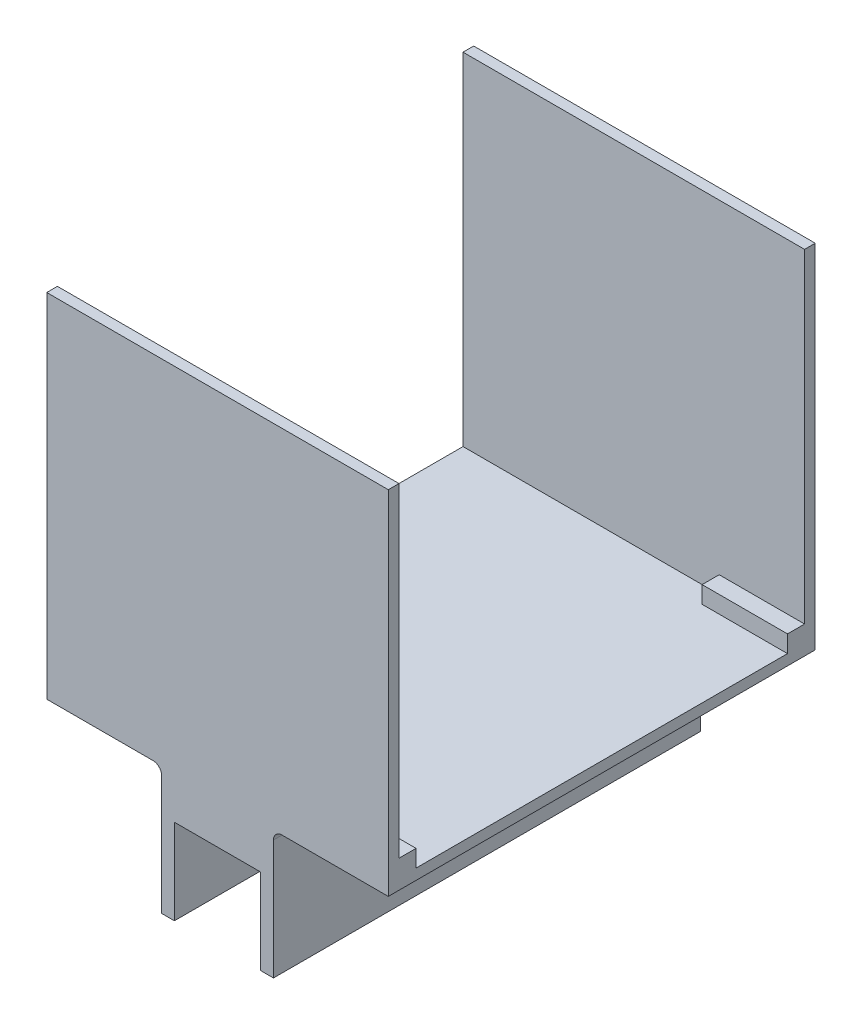
SolidWorks part; units mm, degrees
ref_plane "Front Plane" through (0, 0, 0) normal (0, 0, 1) x (1, 0, 0)
ref_plane "Top Plane" through (0, 0, 0) normal (0, 1, 0) x (1, 0, 0)
ref_plane "Right Plane" through (0, 0, 0) normal (1, 0, 0) x (0, 0, -1)
sketch "Sketch2" plane through (0, 0, 0) normal (0, 0, 1) x (1, 0, 0)
  line L0 (-12.827, -12.7) -> (-16.637, -12.7)
  line L1 (-12.827, -12.7) -> (12.827, -12.7) construction
  line L2 (-12.827, -12.7) -> (-12.827, 12.7)
  line L3 (-12.827, 12.7) -> (12.827, 12.7)
  line L4 (12.827, -12.7) -> (12.827, 12.7)
  line L5 (-12.827, -12.7) -> (12.827, 12.7) construction
  line L6 (-12.827, 12.7) -> (12.827, -12.7) construction
  line L7 (-16.637, -12.7) -> (-16.637, 25.4)
  line L8 (12.827, -12.7) -> (16.637, -12.7)
  line L9 (-16.637, 25.4) -> (16.637, 25.4)
  line L10 (16.637, 25.4) -> (16.637, -12.7)
  point P0 (0, 0)
  dimension "D1" = 25.654
  dimension "D2" = 25.4
  dimension "D3" = 3.81
  dimension "D4" = 38.1
  dimension "D5" = 3.81
extrude "Boss-Extrude1" add sketch "Sketch2" along normal blind 127
sketch "Sketch5" plane through (0, 25.4, 0) normal (0, 1, 0) x (1, 0, 0)
  line L0 (0, 0) -> (0, -127) construction
  line L1 (16.637, -127) -> (-16.637, -127) construction
  line L3 (-50.8, -127) -> (50.8, -127)
  line L4 (-50.8, -127) -> (-50.8, 0)
  line L5 (-50.8, 0) -> (50.8, 0)
  line L6 (50.8, -127) -> (50.8, 0)
  line L7 (-50.8, -127) -> (50.8, 0) construction
  line L8 (-50.8, 0) -> (50.8, -127) construction
  point P5 (0, -63.5)
  dimension "D1" = 101.6
  dimension "D2" = 127
extrude "Boss-Extrude3" add sketch "Sketch5" along normal blind 3.175
fillet "Fillet1" radius 2.54 2 edges at (16.637, 25.4, 63.5) (-16.637, 25.4, 63.5)
sketch "Sketch6" plane through (0, 28.575, 0) normal (0, 1, 0) x (1, 0, 0)
  line L0 (50.8, -127) -> (50.8, 0) construction
  line L1 (-50.8, -127) -> (50.8, -127)
  line L2 (-50.8, -127) -> (-50.8, -123.825)
  line L3 (-50.8, -123.825) -> (50.8, -123.825)
  line L4 (50.8, -127) -> (50.8, -123.825)
  line L6 (-50.8, 0) -> (50.8, 0)
  line L7 (-50.8, 0) -> (-50.8, -3.175)
  line L8 (-50.8, -3.175) -> (50.8, -3.175)
  line L9 (50.8, 0) -> (50.8, -3.175)
  dimension "D1" = 3.175
  dimension "D2" = 3.175
extrude "Boss-Extrude4" add sketch "Sketch6" along normal blind 101.6
sketch "Sketch9" plane through (50.8, 0, 0) normal (1, 0, 0) x (0, 0, -1)
  line L0 (-123.825, 130.175) -> (-123.825, 28.575) construction
  line L1 (-123.825, 28.575) -> (-3.175, 28.575) construction
  line L6 (-3.175, 130.175) -> (-3.175, 28.575) construction
  line L7 (-123.825, 29.9085) -> (-123.825, 28.575)
  line L8 (-123.825, 28.575) -> (-122.4915, 28.575)
  line L11 (-5.3699, 28.575) -> (-3.175, 28.575)
  line L12 (-3.175, 28.575) -> (-3.175, 33.9449)
  line L13 (-123.825, 33.655) -> (-123.825, 29.9085)
  line L14 (-3.175, 28.575) -> (-8.255, 28.575)
  line L15 (-3.175, 28.575) -> (-3.175, 33.655)
  line L16 (-3.175, 33.655) -> (-8.255, 33.655)
  line L17 (-8.255, 28.575) -> (-8.255, 33.655)
  line L18 (-123.825, 28.575) -> (-122.4915, 28.575)
  line L19 (-123.825, 28.575) -> (-123.825, 29.9085)
  line L20 (-123.825, 33.655) -> (-118.745, 33.655)
  line L21 (-118.745, 28.575) -> (-118.745, 33.655)
  line L22 (-118.745, 28.575) -> (-122.4915, 28.575)
  arc A0 (-122.4915, 28.575) -> (-123.825, 29.9085) centre (-122.4915, 29.9085) ccw
  arc A2 (-3.175, 29.9085) -> (-4.5085, 28.575) centre (-4.5085, 29.9085) ccw
  dimension "D1" = 2.667
  dimension "D2" = 2.667
  dimension "D4" = 5.08
  dimension "D5" = 5.08
  dimension "D6" = 5.08
  dimension "D7" = 5.08
extrude "Boss-Extrude6" add sketch "Sketch9" against normal blind 25.4
sketch "Sketch10" plane through (50.8, 0, 0) normal (1, 0, 0) x (0, 0, -1)
  line L0 (-123.825, 29.9085) -> (-123.825, 28.575)
  line L1 (-123.825, 28.575) -> (-122.4915, 28.575)
  line L2 (-127, 25.4) -> (-63.5, 25.4) construction
  line L4 (-63.5, 25.4) -> (-63.5, 100.4541) construction
  arc A0 (-122.4915, 28.575) -> (-123.825, 29.9085) centre (-122.4915, 29.9085) ccw
extrude "Boss-Extrude7" add sketch "Sketch10" against normal blind 0.254
ref_plane "Plane1" through (50.8, 28.575, 3.175) normal (0, 0, -1) x (-1, 0, 0)
sketch "Sketch17" plane through (50.8, 0, 0) normal (1, 0, 0) x (0, 0, -1)
  line L1 (-3.175, 28.575) -> (-8.255, 28.575)
  line L2 (-3.175, 28.575) -> (-3.175, 33.655)
  line L3 (-3.175, 33.655) -> (-8.255, 33.655)
  line L4 (-8.255, 28.575) -> (-8.255, 33.655)
  arc A0 (-3.175, 29.9085) -> (-4.5085, 28.575) centre (-4.5085, 29.9085) ccw
  line M6 (-3.175, 130.175) -> (-3.175, 28.575)
  dimension "D3" = 2.667
  dimension "D1" = 5.08
  dimension "D2" = 5.08
extrude "Boss-Extrude8" add sketch "Sketch17" against normal up to surface (25.4 mm away) contours A0 L3 L4 L1 M6 up to face at (25.4, 31.1956, 121.2044)
sketch "Sketch18" plane through (50.8, 0, 0) normal (1, 0, 0) x (0, 0, -1)
  line L0 (-3.175, 29.9085) -> (-3.175, 28.575) construction
  line L1 (-3.175, 29.9085) -> (-3.175, 28.575)
  line L2 (-4.5085, 28.575) -> (-3.175, 28.575) construction
  line L3 (-4.5085, 28.575) -> (-3.175, 28.575)
  arc A0 (-3.175, 29.9085) -> (-4.5085, 28.575) centre (-4.5085, 29.9085) ccw construction
  arc A1 (-3.175, 29.9085) -> (-4.5085, 28.575) centre (-4.5085, 29.9085) ccw
extrude "Boss-Extrude9" add sketch "Sketch18" against normal up to surface (0.254 mm away) up to face at (50.546, 29.5561, 122.8439)
